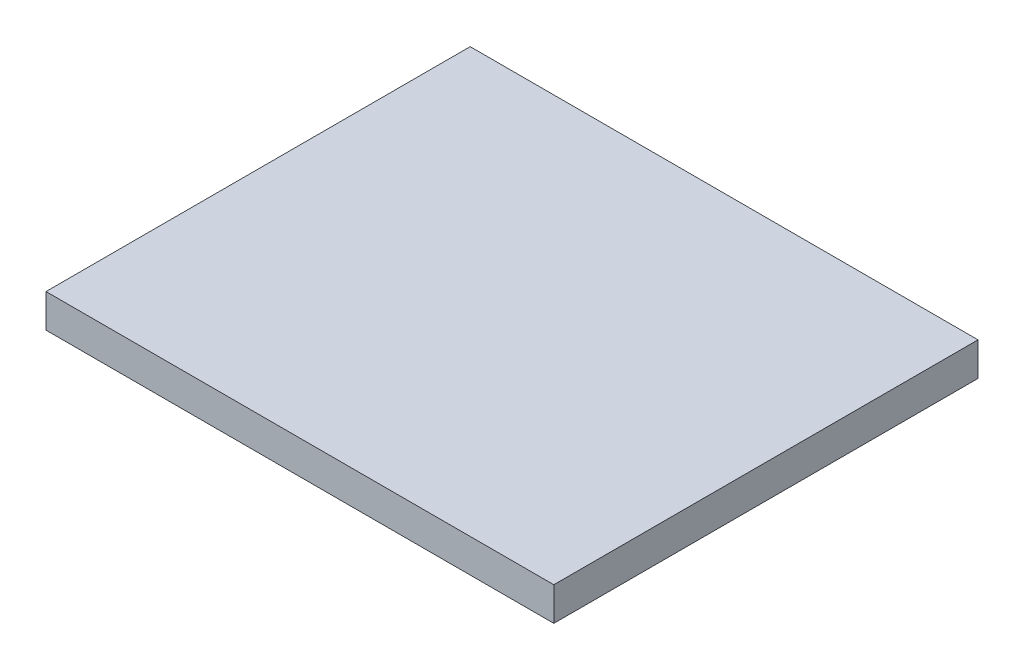
SolidWorks part; units mm, degrees
material "metal_resistor"
ref_plane "Front Plane" through (0, 0, 0) normal (0, 0, 1) x (1, 0, 0)
ref_plane "Top Plane" through (0, 0, 0) normal (0, 1, 0) x (1, 0, 0)
ref_plane "Right Plane" through (0, 0, 0) normal (1, 0, 0) x (0, 0, -1)
sketch "Sketch1" plane through (0, 0, 0) normal (0, 1, 0) x (1, 0, 0)
  line L1 (-7.6928, 3.4261) -> (0.8072, 3.4261)
  line L2 (-7.6928, 3.4261) -> (-7.6928, -3.6739)
  line L3 (-7.6928, -3.6739) -> (0.8072, -3.6739)
  line L4 (0.8072, 3.4261) -> (0.8072, -3.6739)
  dimension "D1" = 8.5
  dimension "D2" = 7.1
sketch "Sketch2" plane through (0, 0, 0) normal (0, 1, 0) x (1, 0, 0)
  line L0 (-7.6928, 3.4261) -> (0.8072, 3.4261)
  line L1 (-7.6928, 3.4261) -> (-7.6928, -3.6739)
  line L2 (-7.6928, -3.6739) -> (0.8072, -3.6739)
  line L3 (0.8072, 3.4261) -> (0.8072, -3.6739)
extrude "Boss-Extrude1" add sketch "Sketch2" along normal blind 0.56
